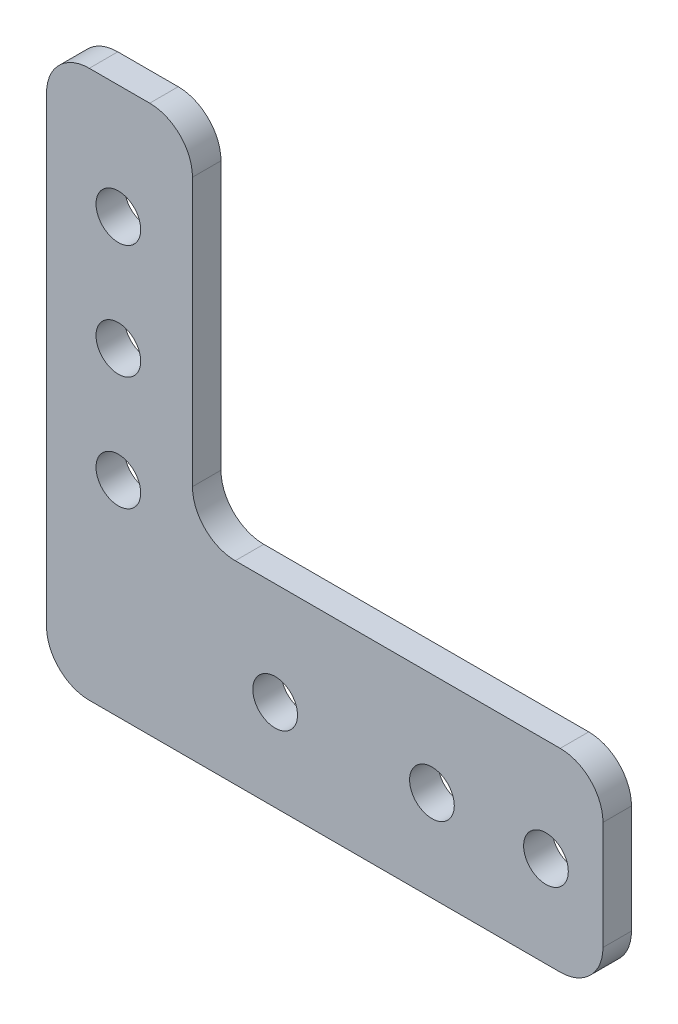
SolidWorks part; units mm, degrees
material "6061-T6 (SS)"
ref_plane "Front Plane" through (0, 0, 0) normal (0, 0, 1) x (1, 0, 0)
ref_plane "Top Plane" through (0, 0, 0) normal (0, 1, 0) x (1, 0, 0)
ref_plane "Right Plane" through (0, 0, 0) normal (1, 0, 0) x (0, 0, -1)
sketch "Sketch1" plane through (0, 0, 0) normal (0, 0, 1) x (1, 0, 0)
  line L1 (-34.925, -31.75) -> (34.925, -31.75)
  line L2 (-34.925, -31.75) -> (-34.925, 31.75)
  line L3 (-34.925, 31.75) -> (34.925, 31.75)
  line L4 (34.925, -31.75) -> (34.925, 31.75)
  line L5 (-34.925, -31.75) -> (34.925, 31.75) construction
  line L6 (-34.925, 31.75) -> (34.925, -31.75) construction
  line L7 (34.925, 31.75) -> (-10.795, 31.75)
  line L8 (34.925, 31.75) -> (34.925, -7.62)
  line L9 (34.925, -7.62) -> (-10.795, -7.62)
  line L10 (-10.795, 31.75) -> (-10.795, -7.62)
  line L11 (-34.925, -31.75) -> (-27.051, -31.75)
  line L12 (-34.925, -31.75) -> (-34.925, 31.75)
  line L13 (-34.925, 31.75) -> (-27.051, 31.75)
  line L14 (-27.051, -31.75) -> (-27.051, 31.75)
  line L15 (-27.051, -31.75) -> (34.925, -31.75)
  line L16 (-27.051, -31.75) -> (-27.051, -29.21)
  line L17 (-27.051, -29.21) -> (34.925, -29.21)
  line L18 (34.925, -31.75) -> (34.925, -29.21)
  circle A0 centre (-19.05, -19.05) radius 2.4892
  circle A1 centre (-19.05, -6.35) radius 2.4892
  circle A2 centre (-19.05, 6.35) radius 2.4892
  circle A3 centre (-19.05, 19.05) radius 2.4892
  circle A4 centre (-1.5875, -19.05) radius 2.4892
  circle A5 centre (15.875, -19.05) radius 2.4892
  circle A6 centre (28.575, -19.05) radius 2.4892
  point P0 (0, 0)
  dimension "D7" = 4.9784
  dimension "D14" = 17.4625
  dimension "D1" = 69.85
  dimension "D2" = 63.5
  dimension "D3" = 24.13
  dimension "D4" = 24.13
  dimension "D5" = 7.874
  dimension "D6" = 63.5
  dimension "D8" = 15.875
  dimension "D9" = 12.7
  dimension "D10" = 12.7
  dimension "D11" = 12.7
  dimension "D12" = 12.7
  dimension "D13" = 12.7
  dimension "D15" = 50.8
  dimension "D16" = 2.54
extrude "Boss-Extrude1" add sketch "Sketch1" along normal blind 3.175 contours L14 L17 L4 L9 L10 L3 A6 A5 A4 A3 A2 A1 A0 | A0
fillet "Fillet1" radius 4.7625 6 edges at (-27.051, 31.75, 1.5875) (-10.795, 31.75, 1.5875) (-10.795, -7.62, 1.5875) (34.925, -7.62, 1.5875) (34.925, -29.21, 1.5875) (-27.051, -29.21, 1.5875)
